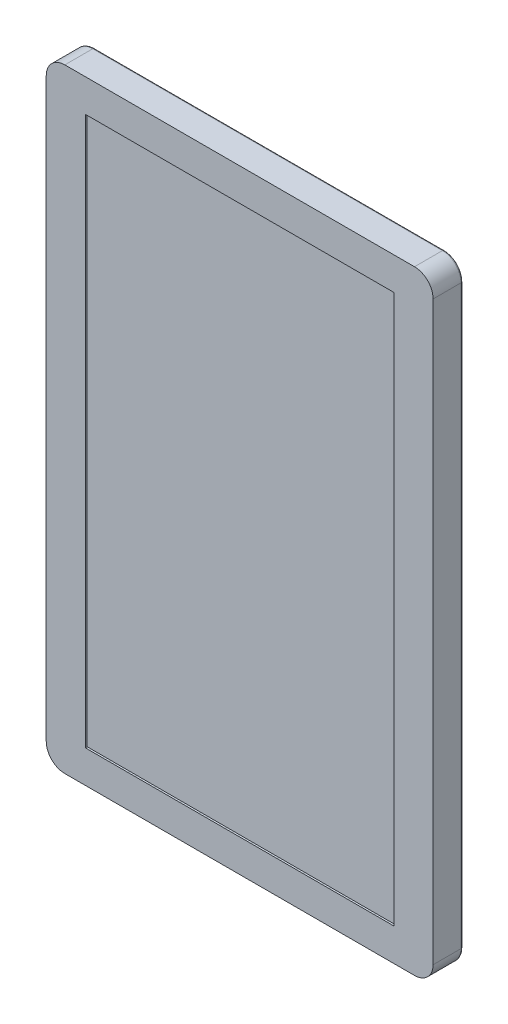
SolidWorks part; units mm, degrees
material "ABS"
ref_plane "Front Plane" through (0, 0, 0) normal (0, 0, 1) x (1, 0, 0)
ref_plane "Top Plane" through (0, 0, 0) normal (0, 1, 0) x (1, 0, 0)
ref_plane "Right Plane" through (0, 0, 0) normal (1, 0, 0) x (0, 0, -1)
sketch "Sketch1" plane through (0, 0, 0) normal (0, 0, 1) x (1, 0, 0)
  line L1 (-94, 165) -> (94, 165)
  line L2 (-104, 155) -> (-104, -155)
  line L3 (-94, -165) -> (94, -165)
  line L4 (104, 155) -> (104, -155)
  line L5 (-104, 165) -> (104, -165) construction
  line L6 (-104, -165) -> (104, 165) construction
  arc A0 (94, -165) -> (104, -155) centre (94, -155) ccw
  arc A1 (-104, -155) -> (-94, -165) centre (-94, -155) ccw
  arc A2 (-94, 165) -> (-104, 155) centre (-94, 155) ccw
  arc A3 (94, 165) -> (104, 155) centre (94, 155) cw
  point P0 (0, 0)
  dimension "D3" = 10
  dimension "D1" = 208
  dimension "D2" = 330
extrude "Boss-Extrude1" add sketch "Sketch1" along normal blind 16
fillet "Fillet2" radius 1 8 edges at (0, 165, 0) (101.0711, 162.0711, 0) (104, 0, 0) (101.0711, -162.0711, 0) (0, -165, 0) (-101.0711, -162.0711, 0) (-104, 0, 0) (-101.0711, 162.0711, 0)
sketch "Sketch2" plane through (0, 0, 16) normal (0, 0, 1) x (1, 0, 0)
  line L1 (-83, 147.5) -> (83, 147.5)
  line L2 (-83, 147.5) -> (-83, -147.5)
  line L3 (-83, -147.5) -> (83, -147.5)
  line L4 (83, 147.5) -> (83, -147.5)
  line L5 (-83, 147.5) -> (83, -147.5) construction
  line L6 (-83, -147.5) -> (83, 147.5) construction
  point P0 (0, 0)
  dimension "D1" = 166
  dimension "D2" = 295
extrude "Cut-Extrude1" cut sketch "Sketch2" against normal blind 1
sketch "Sketch3" plane through (0, 0, 0) normal (0, 0, -1) x (-1, 0, 0)
  line L1 (-50, 50) -> (50, 50) construction
  line L2 (-50, 50) -> (-50, -50) construction
  line L3 (-50, -50) -> (50, -50) construction
  line L4 (50, 50) -> (50, -50) construction
  line L5 (-50, 50) -> (50, -50) construction
  line L6 (-50, -50) -> (50, 50) construction
  circle A0 centre (-50, 50) radius 2.5
  circle A1 centre (50, 50) radius 2.5
  circle A2 centre (50, -50) radius 2.5
  circle A3 centre (-50, -50) radius 2.5
  point P0 (0, 0)
  dimension "D3" = 5
  dimension "D1" = 100
  dimension "D2" = 100
extrude "Cut-Extrude2" cut sketch "Sketch3" against normal blind 10
